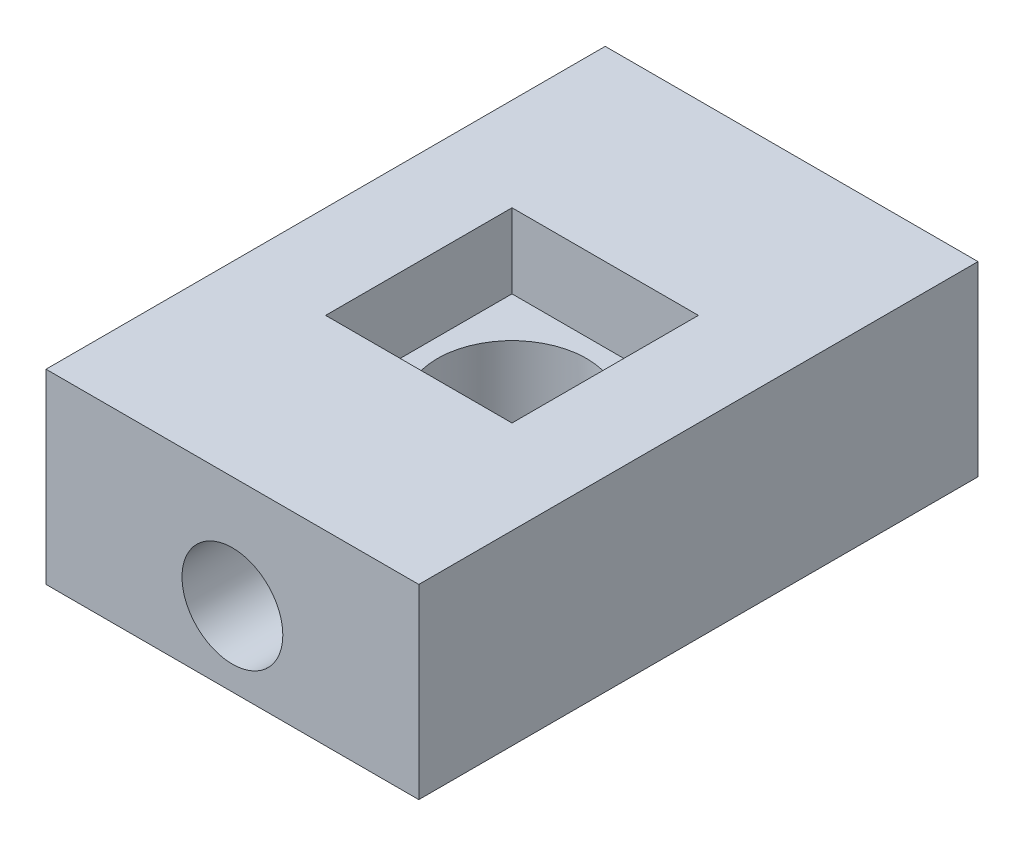
SolidWorks part; units mm, degrees
material "PMMA"
ref_plane "Front Plane" through (0, 0, 0) normal (0, 0, 1) x (1, 0, 0)
ref_plane "Top Plane" through (0, 0, 0) normal (0, 1, 0) x (1, 0, 0)
ref_plane "Right Plane" through (0, 0, 0) normal (1, 0, 0) x (0, 0, -1)
sketch "Sketch1" plane through (0, 0, 0) normal (0, 1, 0) x (1, 0, 0)
  line L1 (10, 15) -> (-10, 15)
  line L2 (10, 15) -> (10, -15)
  line L3 (10, -15) -> (-10, -15)
  line L4 (-10, 15) -> (-10, -15)
  line L5 (10, 15) -> (-10, -15) construction
  line L6 (10, -15) -> (-10, 15) construction
  point P0 (0, 0)
  dimension "D1" = 20
  dimension "D2" = 30
extrude "Boss-Extrude1" add sketch "Sketch1" along normal blind 10
sketch "Sketch2" plane through (0, 10, 0) normal (0, 1, 0) x (1, 0, 0)
  circle A0 centre (0, 0) radius 4
  dimension "D1" = 8
extrude "Cut-Extrude1" cut sketch "Sketch2" against normal blind 8
sketch "Sketch14" plane through (0, 10, 0) normal (0, 1, 0) x (1, 0, 0)
  line L1 (-5, 5) -> (5, 5)
  line L2 (-5, 5) -> (-5, -5)
  line L3 (-5, -5) -> (5, -5)
  line L4 (5, 5) -> (5, -5)
  line L5 (-5, 5) -> (5, -5) construction
  line L6 (-5, -5) -> (5, 5) construction
  point P0 (0, 0)
  dimension "D1" = 10
  dimension "D2" = 10
extrude "Cut-Extrude6" cut sketch "Sketch14" against normal blind 4
sketch "Sketch21" plane through (0, 0, 15) normal (0, 0, 1) x (1, 0, 0)
  line L1 (0, 2) -> (0, 6) construction
  line L2 (4, 2) -> (-4, 2) construction
  line L3 (-5, 6) -> (5, 6) construction
  line L4 (-4, 4) -> (4, 4) construction
  line L5 (-4, 6) -> (-4, 2) construction
  line L6 (4, 2) -> (4, 6) construction
  point P14 (0, 4)
hole_wizard "1/4-28 Tapped Hole2" positions "Sketch23" profile "Sketch22" tap size "1/4-28" standard "ANSI Inch"
sketch "Sketch23" plane through (0, 0, 15) normal (0, 0, 1) x (1, 0, 0)
  point P0 (0, 4)
sketch "Sketch22" plane through (0, 4, 15) normal (1, 0, 0) x (0, -1, 0)
  line L0 (0, 0) -> (0, 8.9)
  line L1 (0, 8.9) -> (2.7051, 8.9)
  line L2 (2.7051, 8.9) -> (2.7051, 0)
  line L5 (2.7051, 0) -> (0, 0)
  line L10 (0, 8.9) -> (-2.7051, 8.9) construction
  line L11 (0, -6.35) -> (0, 107.95) construction
  dimension "Tap Drill Dia." = 5.4102
  dimension "Tap Drill Depth" = 8.9
  dimension "Drill Angle" = 180
cosmetic thread "Hole Thread2" parameters "D1"=8.9, "D2"=6.35
hole_wizard "Ø1.0mm Dowel Hole2" positions "Sketch25" profile "Sketch24" hole size "Ø1.0" standard "ANSI Metric"
sketch "Sketch25" plane through (0, 0, 15) normal (0, 0, 1) x (1, 0, 0)
  point P0 (0, 4)
sketch "Sketch24" plane through (0, 4, 15) normal (1, 0, 0) x (0, -1, 0)
  line L0 (0, 0) -> (0, 21.1)
  line L1 (0, 21.1) -> (0.5, 21.1)
  line L2 (0.5, 21.1) -> (0.5, 0)
  line L5 (0.5, 0) -> (0, 0)
  line L11 (0, -6.35) -> (0, 107.95) construction
  dimension "Thru Hole Dia." = 1
  dimension "Thru Hole Depth" = 21.1
ref_plane "Plane3" through (0, 0, 0) normal (0, 0, 1) x (1, 0, 0)
mirror "Mirror2" about plane through (0, 0, 0) normal (0, 0, 1) of "Ø1.0mm Dowel Hole2", "1/4-28 Tapped Hole2"
